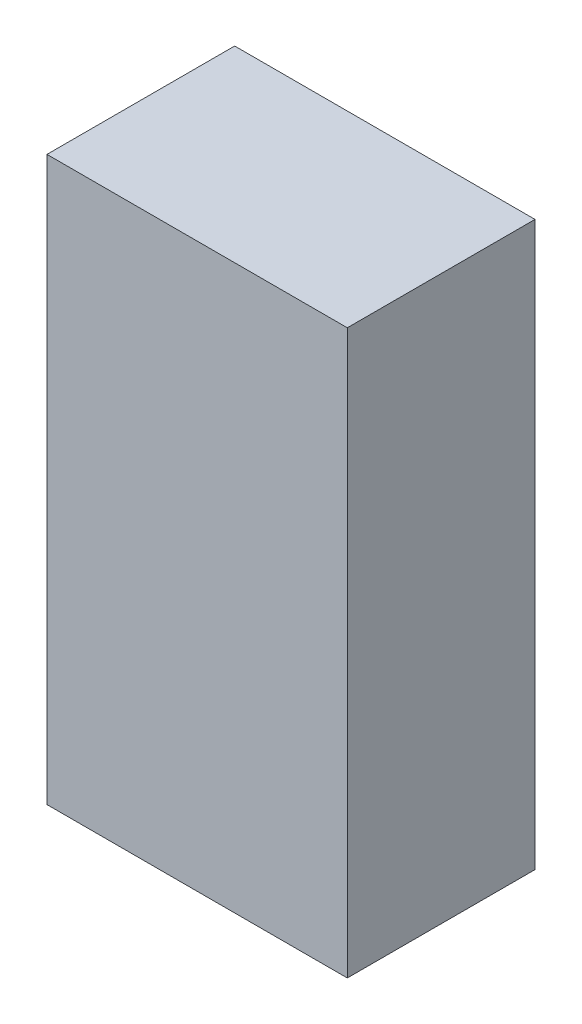
SolidWorks part; units mm, degrees
ref_plane "Přední rovina" through (0, 0, 0) normal (0, 0, 1) x (1, 0, 0)
ref_plane "Horní rovina" through (0, 0, 0) normal (0, 1, 0) x (1, 0, 0)
ref_plane "Pravá rovina" through (0, 0, 0) normal (1, 0, 0) x (0, 0, -1)
sketch "Skica1" plane through (0, 0, 0) normal (0, 0, 1) x (1, 0, 0)
  line L1 (-4, 7.5) -> (4, 7.5)
  line L2 (-4, 7.5) -> (-4, -7.5)
  line L3 (-4, -7.5) -> (4, -7.5)
  line L4 (4, 7.5) -> (4, -7.5)
  line L5 (-4, 7.5) -> (4, -7.5) construction
  line L6 (-4, -7.5) -> (4, 7.5) construction
  point P0 (0, 0)
  dimension "D1" = 8
  dimension "D2" = 15
extrude "Přidat vysunutím1" add sketch "Skica1" along normal blind 5
